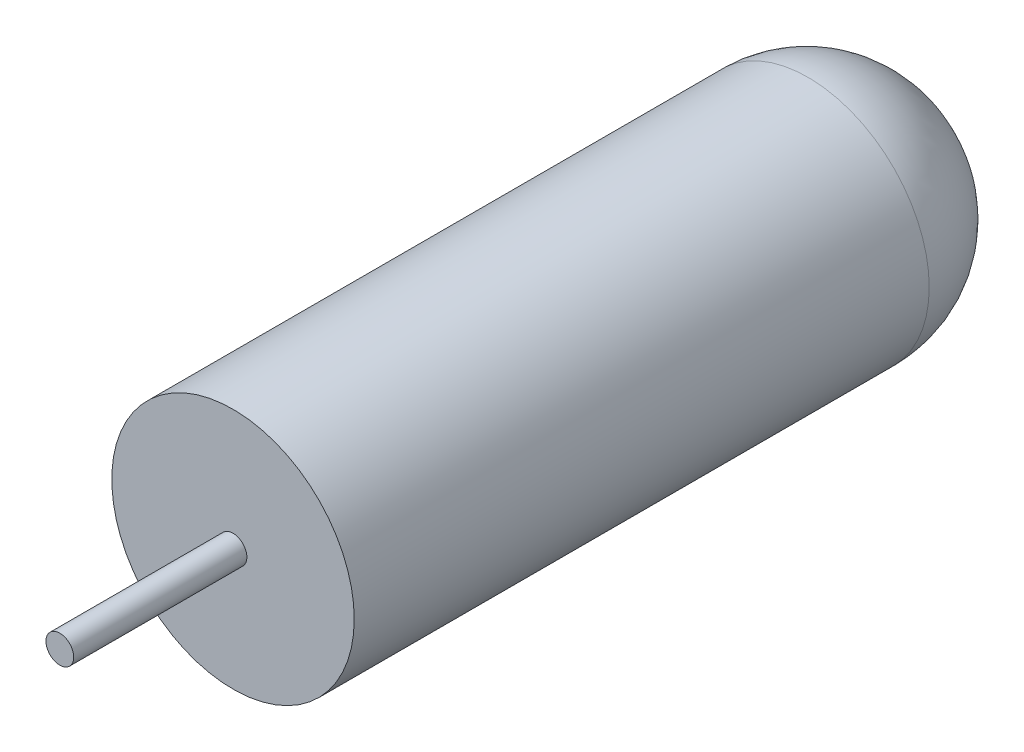
SolidWorks part; units mm, degrees
ref_plane "Plan de face" through (0, 0, 0) normal (0, 0, 1) x (1, 0, 0)
ref_plane "Plan de dessus" through (0, 0, 0) normal (0, 1, 0) x (1, 0, 0)
ref_plane "Plan de droite" through (0, 0, 0) normal (1, 0, 0) x (0, 0, -1)
sketch "Esquisse1" plane through (0, 0, 0) normal (0, 0, 1) x (1, 0, 0)
  circle A0 centre (0, 0) radius 17.5
extrude "Boss.-Extru.1" add sketch "Esquisse1" along normal blind 100
fillet "Congé1" radius 17 1 edges at (17.5, 0, 0)
sketch "Esquisse2" plane through (0, 0, 100) normal (0, 0, 1) x (1, 0, 0)
  circle A0 centre (0, 0) radius 2
extrude "Boss.-Extru.2" add sketch "Esquisse2" along normal blind 25
